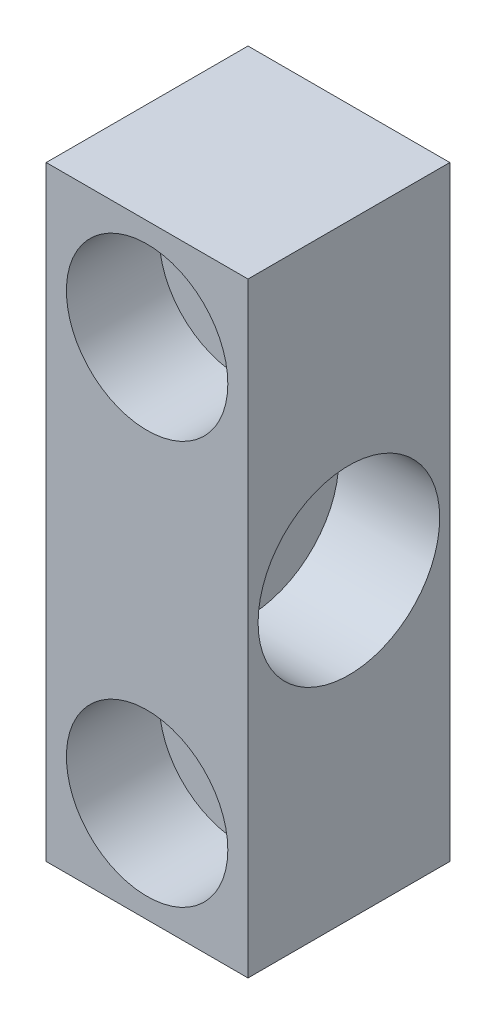
SolidWorks part; units mm, degrees
material "6061 合金"
ref_plane "前视基准面" through (0, 0, 0) normal (0, 0, 1) x (1, 0, 0)
ref_plane "上视基准面" through (0, 0, 0) normal (0, 1, 0) x (1, 0, 0)
ref_plane "右视基准面" through (0, 0, 0) normal (1, 0, 0) x (0, 0, -1)
sketch "草图1" plane through (0, 0, 0) normal (0, 0, 1) x (1, 0, 0)
  line L1 (-5, -15) -> (5, -15)
  line L2 (-5, -15) -> (-5, 15)
  line L3 (-5, 15) -> (5, 15)
  line L4 (5, -15) -> (5, 15)
  line L5 (-5, -15) -> (5, 15) construction
  line L6 (-5, 15) -> (5, -15) construction
  point P0 (0, 0)
  dimension "D1" = 10
  dimension "D2" = 30
extrude "凸台-拉伸1" add sketch "草图1" along normal blind 10
hole_wizard "打孔尺寸(%根据)内六角圆柱头螺钉的类型1" positions "草图3" profile "草图2" counterbore size "M4" standard "GB" end condition through all
sketch "草图3" plane through (0, 0, 10) normal (0, 0, 1) x (1, 0, 0)
  line L0 (5, 15) -> (-5, 15) construction
  point P0 (0, 10)
  point P2 (0, -10)
  dimension "D1" = 20
  dimension "D2" = 5
sketch "草图2" plane through (0, 10, 10) normal (1, 0, 0) x (0, -1, 0)
  line L0 (0, 0) -> (0, 10)
  line L1 (0, 10) -> (2.25, 10)
  line L3 (2.25, 10) -> (2.25, 4.6)
  line L4 (2.25, 4.6) -> (4, 4.6)
  line L5 (4, 4.6) -> (4, 0)
  line L7 (4, 0) -> (0, 0)
  line L11 (0, -6.35) -> (0, 107.95) construction
  dimension "通孔孔直径" = 4.5
  dimension "通孔孔深度" = 10
  dimension "柱形沉头孔直径" = 8
  dimension "柱形沉头孔深度" = 4.6
hole_wizard "M5 螺纹孔1" positions "草图5" profile "草图4" tap size "M5" standard "GB" end condition through all
sketch "草图5" plane through (5, 0, 0) normal (1, 0, 0) x (0, 0, -1)
  point P0 (-5, 0)
  dimension "D1" = 5
sketch "草图4" plane through (5, 0, 5) normal (0, 1, 0) x (0, 0, -1)
  line L0 (0, 0) -> (0, 10)
  line L1 (0, 10) -> (2.1, 10)
  line L2 (2.1, 10) -> (2.1, 0)
  line L5 (2.1, 0) -> (0, 0)
  line L11 (0, -6.35) -> (0, 107.95) construction
  dimension "通孔螺纹孔钻头直径" = 4.2
  dimension "通孔螺纹孔钻头深度" = 10
cosmetic thread "孔螺蚊线1" parameters "D2"=5
sketch "草图6" plane through (5, 0, 0) normal (1, 0, 0) x (0, 0, -1)
  circle A0 centre (-5, 0) radius 4.5
  dimension "D1" = 9
extrude "切除-拉伸1" cut sketch "草图6" against normal blind 5
